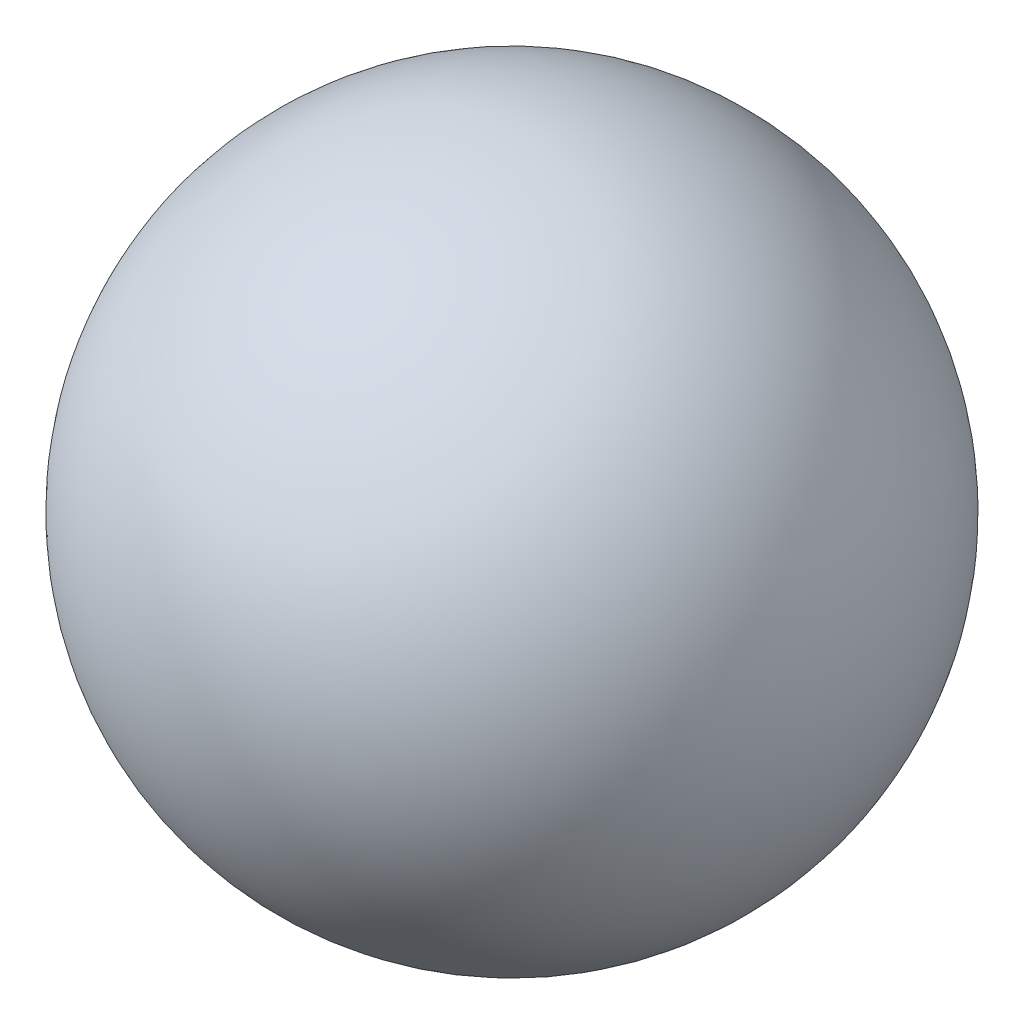
SolidWorks part; units mm, degrees
ref_plane "前基準面" through (0, 0, 0) normal (0, 0, 1) x (1, 0, 0)
ref_plane "上基準面" through (0, 0, 0) normal (0, 1, 0) x (1, 0, 0)
ref_plane "右基準面" through (0, 0, 0) normal (1, 0, 0) x (0, 0, -1)
sketch "草圖1" plane through (0, 0, 0) normal (0, 0, 1) x (1, 0, 0)
  line L0 (-7.5, 0) -> (7.5, 0)
  circle A0 centre (0, 0) radius 7.5
  dimension "D1" = 15
revolve "旋轉1" add sketch "草圖1" angle 360 about L0
